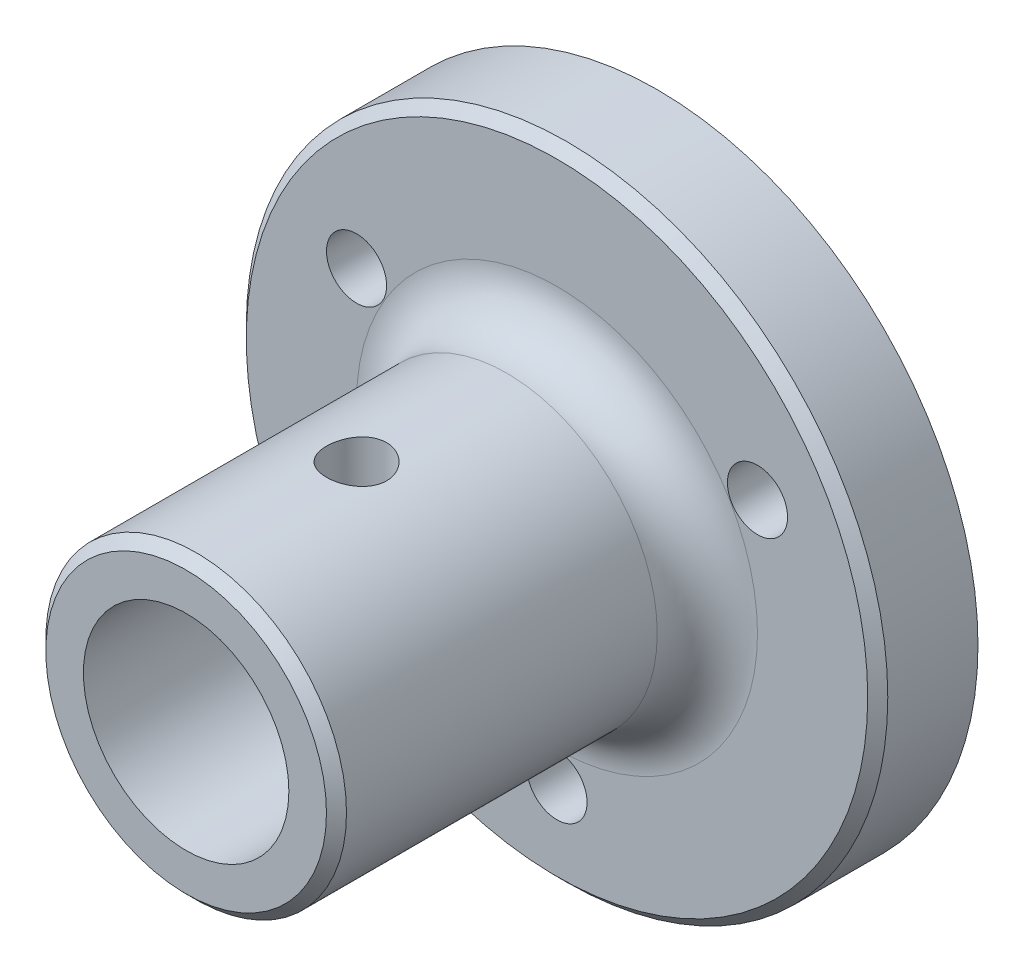
SolidWorks part; units mm, degrees
material "ABS"
ref_plane "Front Plane" through (0, 0, 0) normal (0, 0, 1) x (1, 0, 0)
ref_plane "Top Plane" through (0, 0, 0) normal (0, 1, 0) x (1, 0, 0)
ref_plane "Right Plane" through (0, 0, 0) normal (1, 0, 0) x (0, 0, -1)
sketch "Sketch1" plane through (0, 0, 0) normal (0, 0, 1) x (1, 0, 0)
  line L0 (0, 0) -> (0, -23.094) construction
  line L1 (0, 0) -> (20, 11.547) construction
  line L2 (0, 0) -> (-20, 11.547) construction
  line L3 (20, 11.547) -> (0, -23.094) construction
  line L4 (0, -23.094) -> (-20, 11.547) construction
  line L5 (-20, 11.547) -> (20, 11.547) construction
  circle A0 centre (0, 0) radius 32
  circle A1 centre (20, 11.547) radius 3
  circle A2 centre (0, -23.094) radius 3
  circle A3 centre (-20, 11.547) radius 3
  circle A4 centre (0, 0) radius 10 construction
  dimension "D1" = 64
  dimension "D7" = 6
  dimension "D8" = 6
  dimension "D9" = 6
  dimension "D10" = 20
  dimension "D2" = 40
  dimension "D3" = 40
extrude "Boss-Extrude1" add sketch "Sketch1" along normal blind 10
sketch "Sketch2" plane through (0, 0, 10) normal (0, 0, 1) x (1, 0, 0)
  circle A0 centre (0, 0) radius 10.25
  circle A1 centre (0, 0) radius 15
  dimension "D1" = 20.5
extrude "Boss-Extrude2" add sketch "Sketch2" along normal blind 37
sketch "Sketch3" plane through (0, 0, 0) normal (0, 1, 0) x (1, 0, 0)
  line L0 (0, -10) -> (0, -30)
  line L1 (-15, -10) -> (15, -10) construction
  circle A0 centre (0, -30) radius 3
  dimension "D2" = 6
  dimension "D1" = 20
extrude "Cut-Extrude1" cut sketch "Sketch3" against normal through all both and the other way through all
fillet "圆角1" radius 5 1 edges at (15, 0, 10)
chamfer "倒角1" distance 1 angle 45 2 edges at (15, 0, 47) (32, 0, 10)
